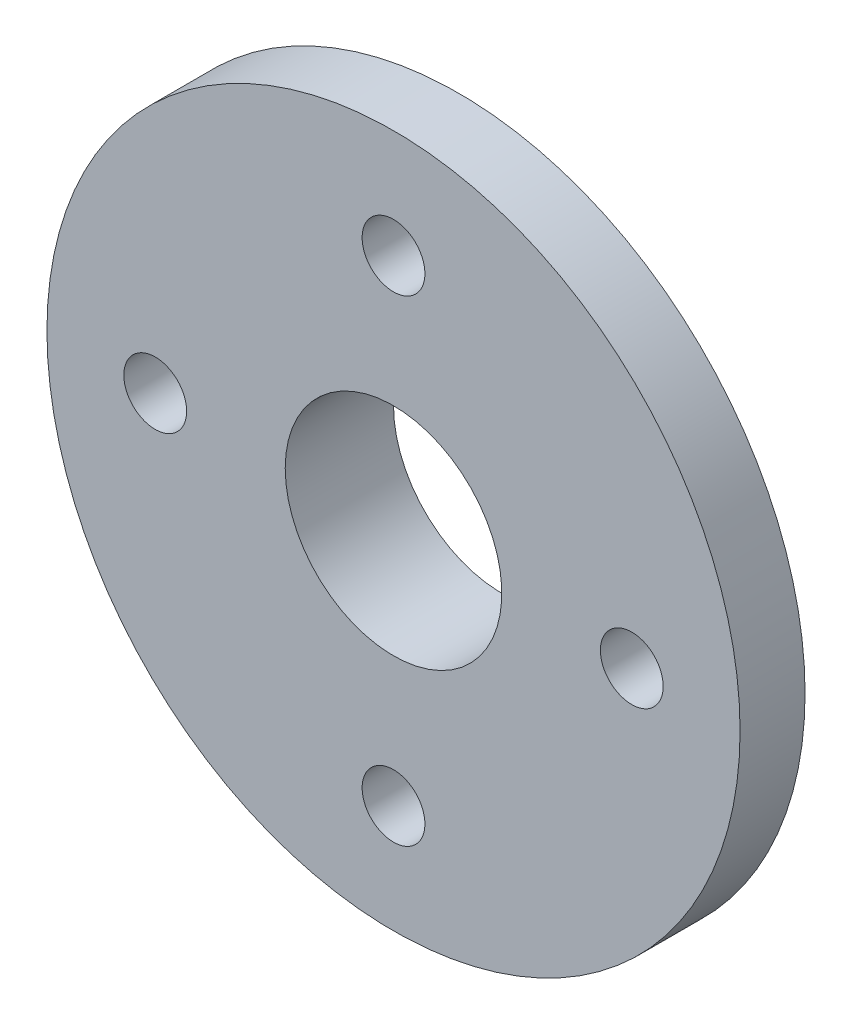
SolidWorks part; units mm, degrees
ref_plane "前视基准面" through (0, 0, 0) normal (0, 0, 1) x (1, 0, 0)
ref_plane "上视基准面" through (0, 0, 0) normal (0, 1, 0) x (1, 0, 0)
ref_plane "右视基准面" through (0, 0, 0) normal (1, 0, 0) x (0, 0, -1)
sketch "草图1" plane through (0, 0, 606.7126) normal (0, 0, -1) x (-1, 0, 0)
  circle A1 centre (-4.2953, -1.2255) radius 5 construction
  circle A3 centre (-4.2953, -1.2255) radius 5
  circle A4 centre (-4.2953, -1.2255) radius 8
  dimension "D1" = 16
extrude "凸台-拉伸1" add sketch "草图1" along normal blind 5
sketch "草图4" plane through (0, 0, 606.7126) normal (0, 0, -1) x (-1, 0, 0)
  circle A1 centre (-4.2953, -1.2255) radius 8 construction
  circle A3 centre (-4.2953, -1.2255) radius 8
  circle A4 centre (-4.2953, -1.2255) radius 16
  dimension "D1" = 32
extrude "凸台-拉伸2" add sketch "草图4" along normal blind 3
sketch "草图5" plane through (0, 0, 603.7126) normal (0, 0, -1) x (-1, 0, 0)
  circle A0 centre (-4.2953, -1.2255) radius 16 construction
  circle A1 centre (-4.2953, -1.2255) radius 16
  circle A2 centre (-4.2953, -1.2255) radius 12.5
  dimension "D1" = 25
extrude "凸台-拉伸3" add sketch "草图5" against normal blind 3
hole_wizard "ST2.9 间隙孔1" positions "草图6" profile "草图7" hole size "ST2.9" standard "GB" end condition through all
sketch "草图6" plane through (0, 0, 603.7126) normal (0, 0, -1) x (-1, 0, 0)
  point P0 (-4.2953, 9.7745)
  point P3 (6.7047, -1.2255)
  point P6 (-4.2953, -12.2255)
  point P9 (-15.2953, -1.2255)
sketch "草图7" plane through (4.2953, 9.7745, 603.7126) normal (1, 0, 0) x (0, 1, 0)
  line L0 (0, 0) -> (0, 3)
  line L1 (0, 3) -> (1.45, 3)
  line L2 (1.45, 3) -> (1.45, 0)
  line L5 (1.45, 0) -> (0, 0)
  line L11 (0, -6.35) -> (0, 107.95) construction
  dimension "通孔孔直径" = 2.9
  dimension "通孔孔深度" = 3
